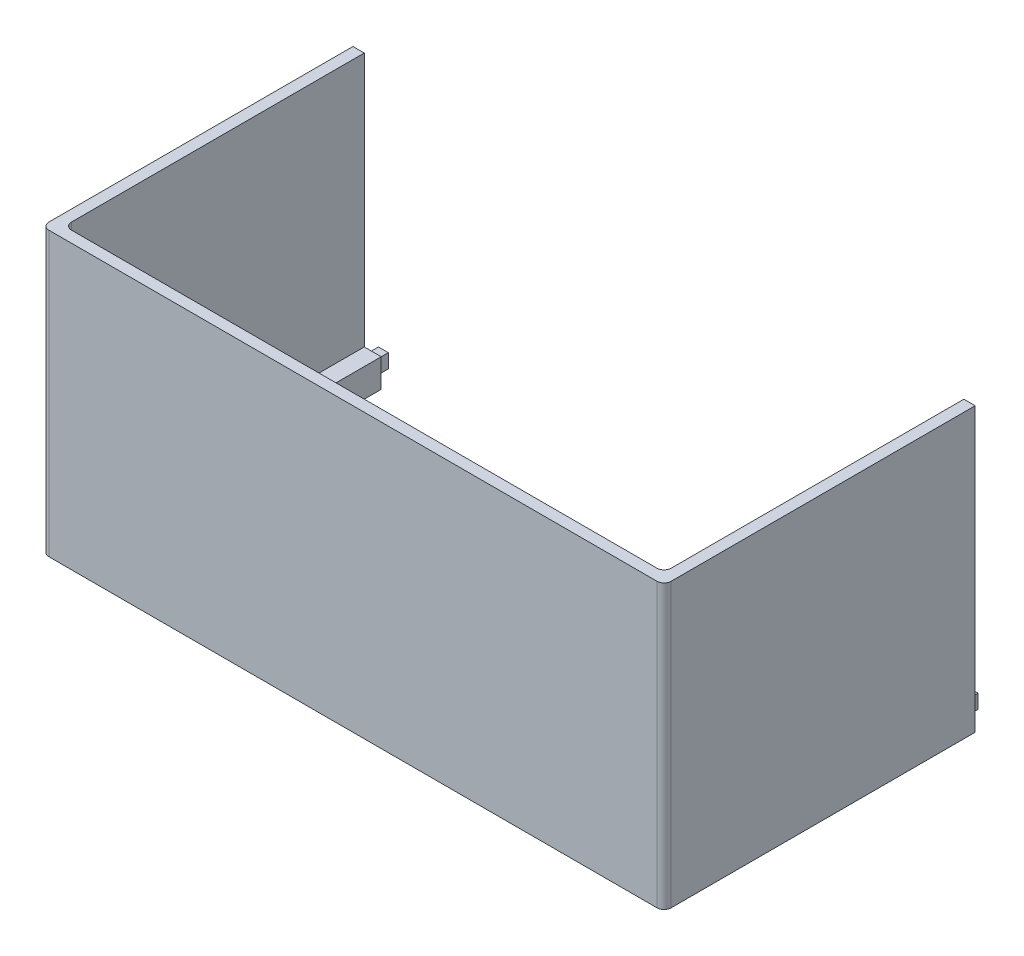
SolidWorks part; units mm, degrees
ref_plane "Front Plane" through (0, 0, 0) normal (0, 0, 1) x (1, 0, 0)
ref_plane "Top Plane" through (0, 0, 0) normal (0, 1, 0) x (1, 0, 0)
ref_plane "Right Plane" through (0, 0, 0) normal (1, 0, 0) x (0, 0, -1)
sketch "Sketch1" plane through (0, 0, 0) normal (0, 1, 0) x (1, 0, 0)
  line L1 (-69.85, -77.1042) -> (69.85, -77.1042)
  line L2 (-69.85, -77.1042) -> (-69.85, 77.1042)
  line L3 (-69.85, 77.1042) -> (69.85, 77.1042)
  line L4 (69.85, -77.1042) -> (69.85, 77.1042)
  line L5 (-69.85, -77.1042) -> (69.85, 77.1042) construction
  line L6 (-69.85, 77.1042) -> (69.85, -77.1042) construction
  point P0 (0, 0)
  dimension "D1" = 154.2085
  dimension "D2" = 139.7
extrude "Boss-Extrude1" add sketch "Sketch1" along normal blind 6.35
sketch "Sketch2" plane through (0, 6.35, 0) normal (0, 1, 0) x (1, 0, 0)
  line L0 (69.85, 77.1042) -> (-69.85, 77.1042) construction
  line L1 (-63.5, -70.7542) -> (63.5, -70.7542)
  line L2 (-63.5, -70.7542) -> (-63.5, 70.7542)
  line L3 (-63.5, 70.7542) -> (63.5, 70.7542)
  line L4 (63.5, -70.7542) -> (63.5, 70.7542)
  line L5 (-63.5, -70.7542) -> (63.5, 70.7542) construction
  line L6 (-63.5, 70.7542) -> (63.5, -70.7542) construction
  line L7 (69.85, -77.1042) -> (69.85, 77.1042) construction
  point P0 (0, 0)
  dimension "D1" = 6.35
  dimension "D2" = 6.35
extrude "Cut-Extrude1" cut sketch "Sketch2" against normal blind 6.35
sketch "Sketch3" plane through (0, 6.35, 0) normal (0, 1, 0) x (1, 0, 0)
  line L1 (-69.85, 77.1042) -> (69.85, 77.1042)
  line L2 (-69.85, 77.1042) -> (-69.85, -77.1042)
  line L3 (-69.85, -77.1042) -> (69.85, -77.1042)
  line L4 (69.85, 77.1042) -> (69.85, -77.1042)
  line L5 (-69.85, 77.1042) -> (69.85, -77.1042) construction
  line L6 (-69.85, -77.1042) -> (69.85, 77.1042) construction
  line L7 (-67.31, 74.5642) -> (67.31, 74.5642)
  line L8 (-67.31, 74.5642) -> (-67.31, -74.5642)
  line L9 (-67.31, -74.5642) -> (67.31, -74.5642)
  line L10 (67.31, 74.5642) -> (67.31, -74.5642)
  line L11 (-67.31, 74.5642) -> (67.31, -74.5642) construction
  line L12 (-67.31, -74.5642) -> (67.31, 74.5642) construction
  point P0 (0, 0)
  point P7 (0, 0)
  dimension "D1" = 2.54
  dimension "D2" = 2.54
extrude "Boss-Extrude2" add sketch "Sketch3" along normal blind 57.15
sketch "Sketch4" plane through (0, 63.5, 0) normal (0, 1, 0) x (1, 0, 0)
  line L1 (-69.85, 77.1042) -> (69.85, 77.1042)
  line L2 (-69.85, 77.1042) -> (-69.85, -7.2542)
  line L3 (-69.85, -7.2542) -> (69.85, -7.2542)
  line L4 (69.85, 77.1042) -> (69.85, -7.2542)
  dimension "D1" = 84.3585
extrude "Cut-Extrude2" cut sketch "Sketch4" against normal through all contours L3 L4 L1 L2
sketch "Sketch5" plane through (0, 0, 7.2542) normal (0, 0, -1) x (-1, 0, 0)
  line L0 (-67.31, 6.35) -> (-67.31, 63.5) construction
  line L1 (-67.31, 4.7625) -> (-65.0875, 4.7625)
  line L2 (-67.31, 4.7625) -> (-67.31, 1.5875)
  line L3 (-67.31, 1.5875) -> (-65.0875, 1.5875)
  line L4 (-65.0875, 4.7625) -> (-65.0875, 1.5875)
  line L5 (-67.31, 6.35) -> (-63.5, 6.35) construction
  line L6 (-63.5, 0) -> (-69.85, 0) construction
  line L7 (-63.5, 0) -> (-63.5, 6.35) construction
  line L8 (0, 0) -> (0, 25.1433) construction
  line L9 (63.5, 0) -> (-63.5, 0) construction
  line L10 (65.0875, 4.7625) -> (65.0875, 1.5875)
  line L11 (67.31, 1.5875) -> (65.0875, 1.5875)
  line L12 (67.31, 4.7625) -> (67.31, 1.5875)
  line L13 (67.31, 4.7625) -> (65.0875, 4.7625)
  dimension "D1" = 0
  dimension "D2" = 1.5875
  dimension "D3" = 1.5875
  dimension "D4" = 1.5875
extrude "Boss-Extrude3" add sketch "Sketch5" along normal blind 3.175
fillet "Fillet1" radius 1.5875 4 edges at (-69.85, 31.75, 77.1042) (-67.31, 34.925, 74.5642) (67.31, 34.925, 74.5642) (69.85, 31.75, 77.1042)
